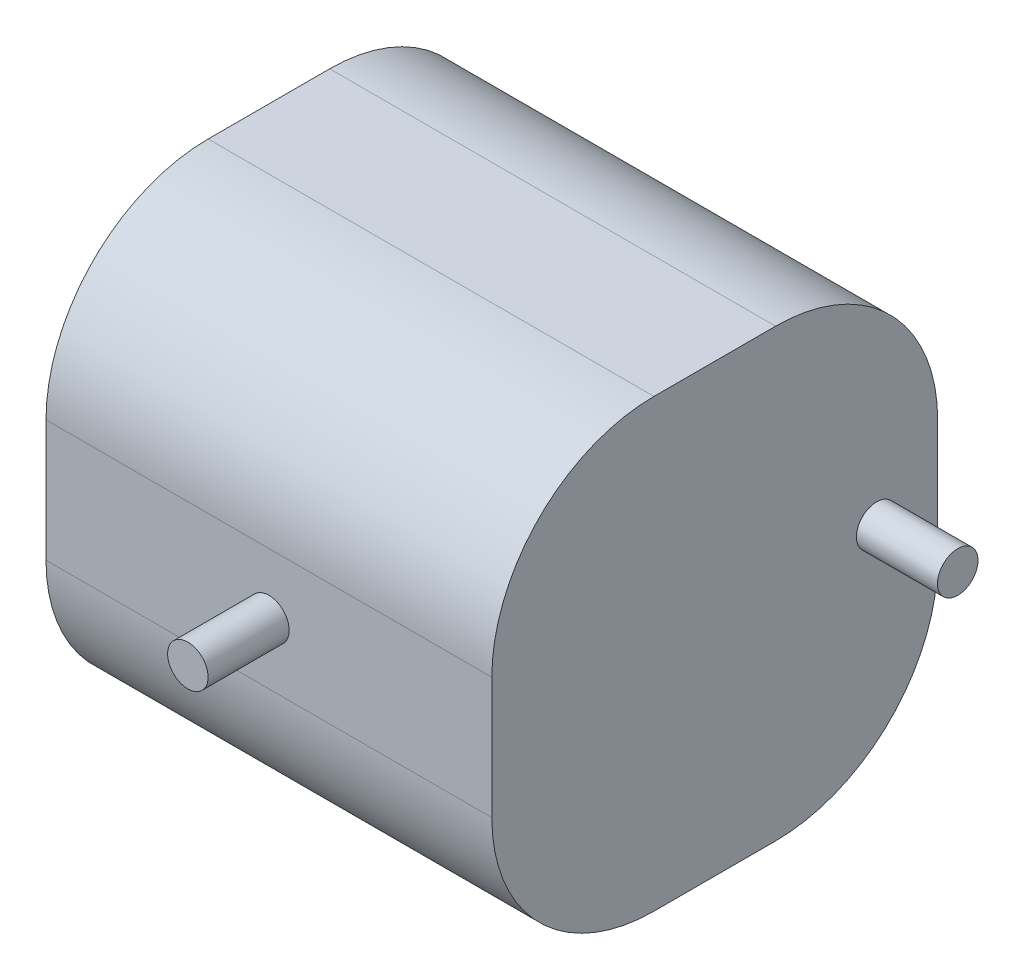
SolidWorks part; units mm, degrees
ref_plane "Спереди" through (0, 0, 0) normal (0, 0, 1) x (1, 0, 0)
ref_plane "Сверху" through (0, 0, 0) normal (0, 1, 0) x (1, 0, 0)
ref_plane "Справа" through (0, 0, 0) normal (1, 0, 0) x (0, 0, -1)
sketch "Эскиз1" plane through (0, 0, 0) normal (0, 0, 1) x (1, 0, 0)
  line L1 (-39.0239, 32.5402) -> (15.9761, 32.5402)
  line L2 (-39.0239, 32.5402) -> (-39.0239, -22.4598)
  line L3 (-39.0239, -22.4598) -> (15.9761, -22.4598)
  line L4 (15.9761, 32.5402) -> (15.9761, -22.4598)
extrude "Бобышка-Вытянуть1" add sketch "Эскиз1" along normal blind 55 contours L1 L4 L3 L2
sketch "Эскиз2" plane through (15.9761, 0, 0) normal (1, 0, 0) x (0, 0, -1)
  circle A0 centre (-7.5236, 5.0402) radius 2.5
extrude "Бобышка-Вытянуть2" add sketch "Эскиз2" along normal blind 10 contours A0
sketch "Эскиз3" plane through (0, 0, 55) normal (0, 0, 1) x (1, 0, 0)
  line L1 (15.9761, -22.4598) -> (15.9761, 32.5402)
  circle A0 centre (-11.5239, 5.0402) radius 2.5
extrude "Бобышка-Вытянуть3" add sketch "Эскиз3" along normal blind 10 contours A0
fillet "Скругление1" radius 20 4 edges at (-11.5239, -22.4598, 0) (-11.5239, -22.4598, 55) (-11.5239, 32.5402, 0) (-11.5239, 32.5402, 55)
